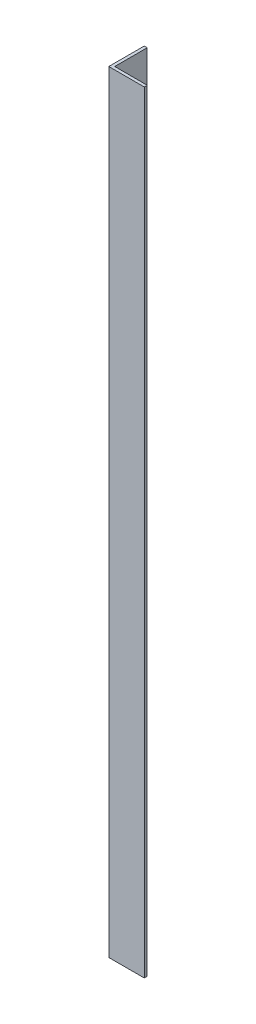
SolidWorks part; units mm, degrees
ref_plane "Front" through (0, 0, 0) normal (0, 0, 1) x (1, 0, 0)
ref_plane "Top" through (0, 0, 0) normal (0, 1, 0) x (1, 0, 0)
ref_plane "Right" through (0, 0, 0) normal (1, 0, 0) x (0, 0, -1)
sketch "Sketch1" plane through (0, 0, 0) normal (0, 1, 0) x (1, 0, 0)
  line L0 (0, 0) -> (19.05, 0)
  line L1 (0, 0) -> (0, 19.05)
  line L2 (1.5875, 1.5875) -> (1.5875, 19.05)
  line L3 (1.5875, 1.5875) -> (19.05, 1.5875)
  line L4 (0, 19.05) -> (1.5875, 19.05)
  line L5 (19.05, 1.5875) -> (19.05, 0)
extrude "Boss-Extrude1" add sketch "Sketch1" along normal blind 414.3375
